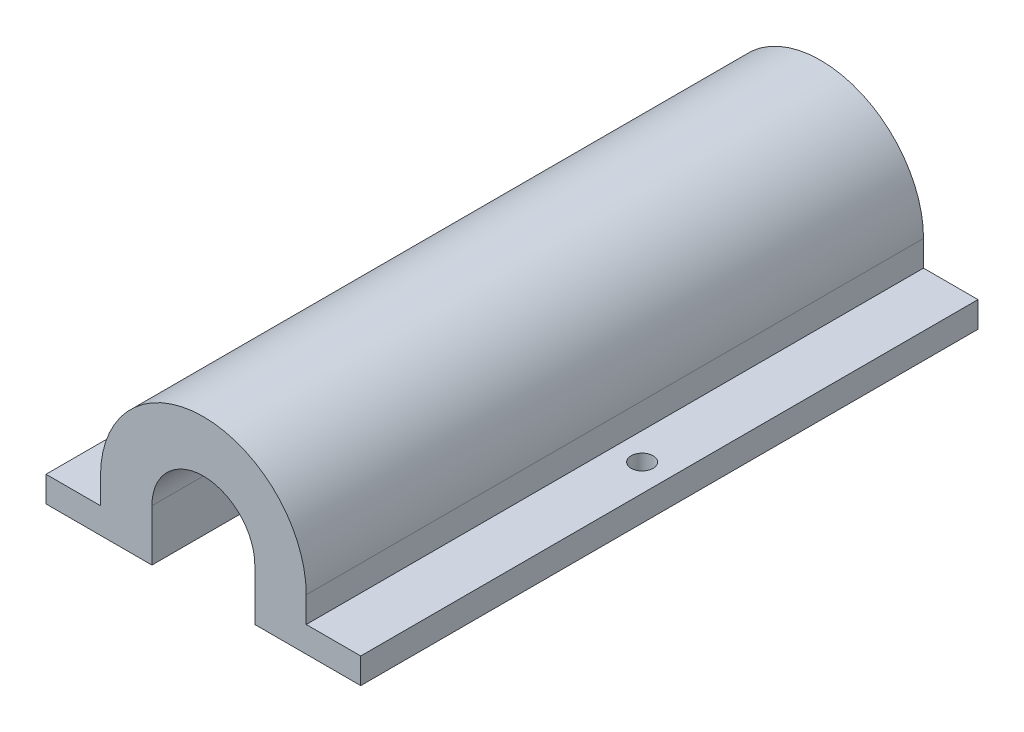
SolidWorks part; units mm, degrees
material "ABS"
ref_plane "Front Plane" through (0, 0, 0) normal (0, 0, 1) x (1, 0, 0)
ref_plane "Top Plane" through (0, 0, 0) normal (0, 1, 0) x (1, 0, 0)
ref_plane "Right Plane" through (0, 0, 0) normal (1, 0, 0) x (0, 0, -1)
sketch "Sketch2" plane through (0, 0, 0) normal (0, 0, 1) x (1, 0, 0)
  line L0 (-19.4259, -6.35) -> (-6.35, -6.35)
  line L3 (-6.35, 0) -> (-6.35, -6.35)
  line L4 (6.35, 0) -> (6.35, -6.35)
  line L5 (6.35, -6.35) -> (19.4259, -6.35)
  line L6 (-19.4259, -6.35) -> (-19.4259, -3.175)
  line L7 (-19.4259, -3.175) -> (-12.7, -3.175)
  line L8 (-12.7, -3.175) -> (-12.7, 0)
  line L9 (19.4259, -6.35) -> (19.4259, -3.175)
  line L10 (19.4259, -3.175) -> (12.7, -3.175)
  line L11 (12.7, -3.175) -> (12.7, 0)
  line L12 (0, 0) -> (0, 20.8456) construction
  arc A0 (6.35, 0) -> (-6.35, 0) centre (0, 0) ccw
  arc A1 (12.7, 0) -> (-12.7, 0) centre (0, 0) ccw
  point P7 (0, -6.35)
  dimension "D1" = 12.7
  dimension "D2" = 12.7
  dimension "D3" = 19.4259
  dimension "D4" = 3.175
  dimension "D5" = 19.4259
extrude "Boss-Extrude1" add sketch "Sketch2" along normal blind 76.2
hole_wizard "Tap Drill for #6-32 Tap1" positions "Sketch3" profile "Sketch4" hole size "#6-32" standard "ANSI Inch" end condition through all
sketch "Sketch3" plane through (0, -3.175, 0) normal (0, 1, 0) x (1, 0, 0)
  point P0 (-16.0629, -38.1)
  point P2 (16.0629, -38.1)
sketch "Sketch4" plane through (-16.0629, -3.175, 38.1) normal (1, 0, 0) x (0, 0, 1)
  line L0 (0, 0) -> (0, 3.175)
  line L1 (0, 3.175) -> (1.3525, 3.175)
  line L2 (1.3525, 3.175) -> (1.3525, 0)
  line L5 (1.3525, 0) -> (0, 0)
  line L11 (0, -6.35) -> (0, 107.95) construction
  dimension "Thru Hole Dia." = 2.7051
  dimension "Thru Hole Depth" = 3.175
